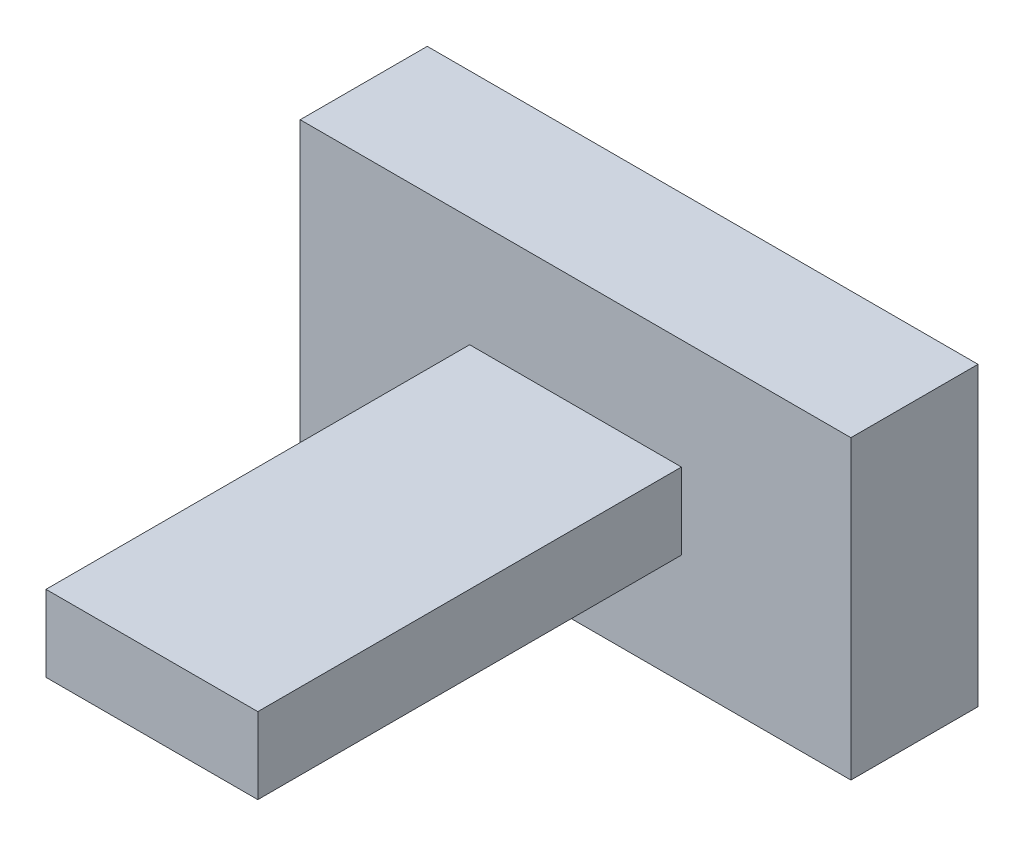
SolidWorks part; units mm, degrees
ref_plane "Plan de face" through (0, 0, 0) normal (0, 0, 1) x (1, 0, 0)
ref_plane "Plan de dessus" through (0, 0, 0) normal (0, 1, 0) x (1, 0, 0)
ref_plane "Plan de droite" through (0, 0, 0) normal (1, 0, 0) x (0, 0, -1)
sketch "Esquisse2" plane through (0, 0, 0) normal (0, 0, 1) x (1, 0, 0)
  line L1 (0, 0) -> (13, 0)
  line L2 (0, 0) -> (0, 7)
  line L3 (0, 7) -> (13, 7)
  line L4 (13, 0) -> (13, 7)
  dimension "D1" = 13
  dimension "D2" = 7
extrude "Boss.-Extru.1" add sketch "Esquisse2" along normal blind 3
sketch "Esquisse4" plane through (0, 0, 3) normal (0, 0, 1) x (1, 0, 0)
  line L0 (0, 7) -> (0, 0) construction
  line L1 (4, 4.4) -> (9, 4.4)
  line L2 (4, 4.4) -> (4, 2.6)
  line L3 (4, 2.6) -> (9, 2.6)
  line L4 (9, 4.4) -> (9, 2.6)
  line L5 (0, 0) -> (13, 0) construction
  point P10 (6.5, 2.6)
  point P11 (6.5, 0)
  point P12 (4, 3.5)
  point P13 (0, 3.5)
  dimension "D1" = 5
  dimension "D2" = 1.8
extrude "Boss.-Extru.2" add sketch "Esquisse4" along normal blind 10
